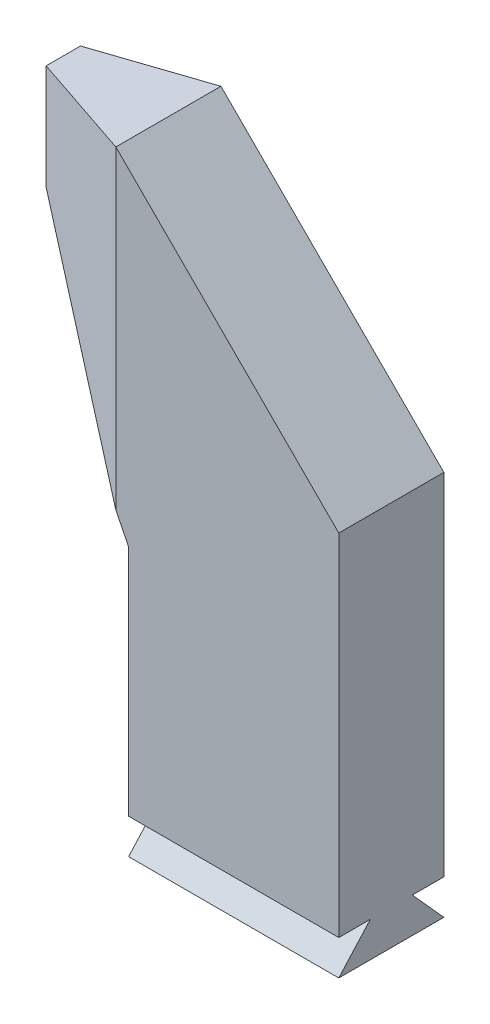
SolidWorks part; units mm, degrees
ref_plane "Front Plane" through (0, 0, 0) normal (0, 0, 1) x (1, 0, 0)
ref_plane "Top Plane" through (0, 0, 0) normal (0, 1, 0) x (1, 0, 0)
ref_plane "Right Plane" through (0, 0, 0) normal (1, 0, 0) x (0, 0, -1)
sketch "Sketch1" plane through (0, 0, 0) normal (0, 0, 1) x (1, 0, 0)
  line L0 (30, 0) -> (30, 100)
  line L1 (30, 100) -> (-33.6396, 163.6396)
  line L2 (-33.6396, 163.6396) -> (-63.6396, 163.6396)
  line L3 (-30, 66.607) -> (-30, 0)
  line L4 (-30, 0) -> (30, 0)
  line L5 (-63.6396, 163.6396) -> (-63.6396, 133.6396)
  line L6 (-63.6396, 133.6396) -> (-30, 66.607)
  point P7 (0, 0)
  dimension "D1" = 60
  dimension "D2" = 90
  dimension "D3" = 30
  dimension "D4" = 75
  dimension "D5" = 100
  dimension "D6" = 30
extrude "Boss-Extrude1" add sketch "Sketch1" along normal mid plane 30
sketch "Sketch2" plane through (30, 0, 0) normal (1, 0, 0) x (0, 0, -1)
  line L0 (-15, -10) -> (15, -10)
  line L1 (15, -10) -> (6, 0)
  line L2 (-15, 0) -> (15, 0) construction
  line L3 (6, 0) -> (-6, 0)
  line L4 (-6, 0) -> (-15, -10)
  point P10 (0, -10)
  dimension "D1" = 12
  dimension "D2" = 9
  dimension "D3" = 10
  dimension "D4" = 30
extrude "Boss-Extrude2" add sketch "Sketch2" against normal up to surface (60 mm away) up to face at (-30, 33.3035, 0)
sketch "Sketch3" plane through (0, 163.6396, 0) normal (0, 1, 0) x (1, 0, 0)
  line L0 (-63.6396, 4.9046) -> (-33.6396, 15)
  line L1 (-63.6396, -15) -> (-63.6396, 15) construction
  line L2 (30, 15) -> (-33.6396, 15) construction
  line L3 (-33.6396, 15) -> (-33.6396, 32.9191)
  line L4 (-33.6396, 32.9191) -> (-75.2087, 32.9191)
  line L5 (-75.2087, 32.9191) -> (-75.2087, 4.9046)
  line L6 (-75.2087, 4.9046) -> (-63.6396, 4.9046)
  line L7 (-63.6396, 0) -> (-53.102, 0) construction
  line L8 (-75.2087, -32.9191) -> (-75.2087, -4.9046)
  line L9 (-33.6396, -32.9191) -> (-75.2087, -32.9191)
  line L10 (-33.6396, -15) -> (-33.6396, -32.9191)
  line L11 (-63.6396, -4.9046) -> (-33.6396, -15)
  line L12 (-75.2087, -4.9046) -> (-63.6396, -4.9046)
  line L13 (-33.6396, -15) -> (-33.6396, 15) construction
extrude "Cut-Extrude1" cut sketch "Sketch3" against normal through all
scale "Scale1" bodies to scale 103 scale about centroid uniform scaling yes scale factor 0.3
